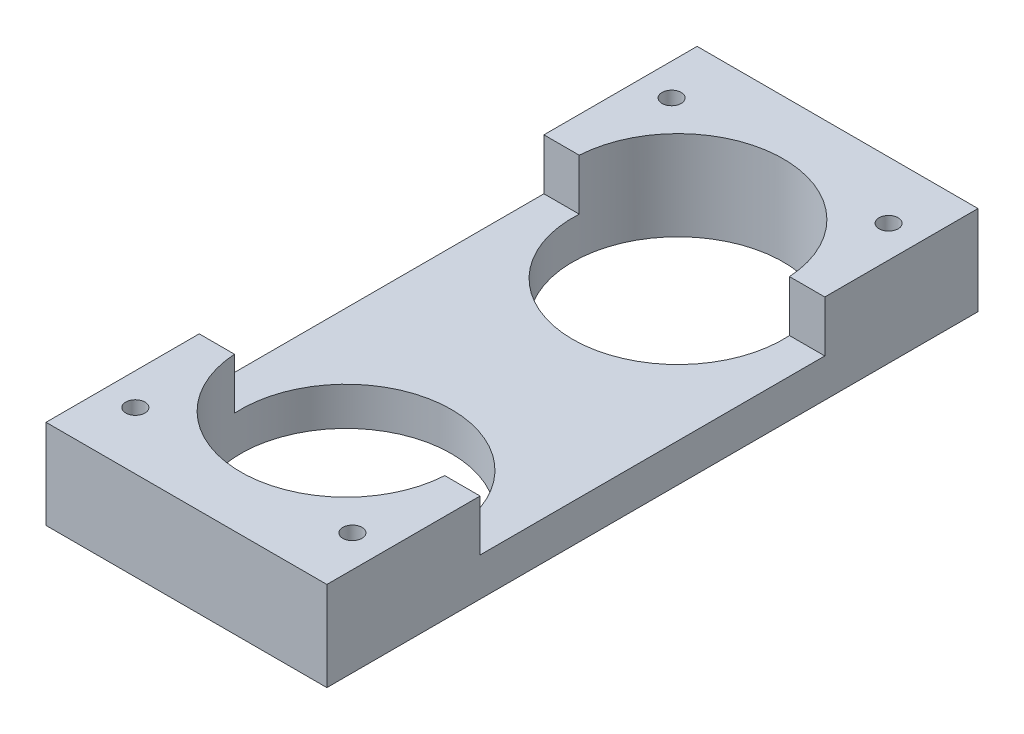
SolidWorks part; units mm, degrees
ref_plane "前视基准面" through (0, 0, 0) normal (0, 0, 1) x (1, 0, 0)
ref_plane "上视基准面" through (0, 0, 0) normal (0, 1, 0) x (1, 0, 0)
ref_plane "右视基准面" through (0, 0, 0) normal (1, 0, 0) x (0, 0, -1)
sketch "草图1" plane through (0, 0, 0) normal (0, 1, 0) x (1, 0, 0)
  line L1 (11, 25.5) -> (-11, 25.5)
  line L2 (11, 25.5) -> (11, -25.5)
  line L3 (11, -25.5) -> (-11, -25.5)
  line L4 (-11, 25.5) -> (-11, -25.5)
  line L5 (11, 25.5) -> (-11, -25.5) construction
  line L6 (11, -25.5) -> (-11, 25.5) construction
  point P0 (0, 0)
  dimension "D1" = 22
  dimension "D2" = 51
extrude "底座" add sketch "草图1" along normal blind 3
sketch "草图2" plane through (0, 3, 0) normal (0, 1, 0) x (1, 0, 0)
  line L0 (-11, 25.5) -> (-11, -25.5) construction
  line L1 (11, 13.5) -> (-11, 13.5)
  line L2 (11, 13.5) -> (11, -13.5)
  line L3 (11, -13.5) -> (-11, -13.5)
  line L4 (-11, 13.5) -> (-11, -13.5)
  line L5 (11, 13.5) -> (-11, -13.5) construction
  line L6 (11, -13.5) -> (-11, 13.5) construction
  point P0 (0, 0)
  line M2 (-11, 25.5) -> (-11, -25.5)
  line M3 (-11, -25.5) -> (11, -25.5)
  line M4 (11, -25.5) -> (11, 25.5)
  line M5 (11, 25.5) -> (-11, 25.5)
  dimension "D1" = 27
extrude "高台" add sketch "草图2" along normal blind 4 contours L3 M4 M2 M3 | L1 M4 M5 M2
sketch "草图3" plane through (0, 0, 0) normal (0, -1, 0) x (1, 0, 0)
  line L0 (11, 0) -> (-11, 0)
  line L1 (-11, -25.5) -> (-11, 25.5) construction
  circle A0 centre (0, 13) radius 8.25
  circle A1 centre (0, -13) radius 8.25
  point P8 (0, 0)
  dimension "D1" = 16.5
  dimension "D2" = 13
extrude "穿孔" cut sketch "草图3" against normal through all contours A0 | A1
sketch "草图4" plane through (0, 7, 0) normal (0, 1, 0) x (1, 0, 0)
  line L0 (11, 0) -> (-11, 0)
  line L1 (-11, 13.5) -> (-11, -13.5) construction
  line L2 (0, 25.5) -> (0, -25.5)
  line L3 (-11, -25.5) -> (11, -25.5) construction
  circle A0 centre (-8.5, -21) radius 0.75
  circle A1 centre (8.5, -21) radius 0.75
  circle A2 centre (8.5, 21) radius 0.75
  circle A3 centre (-8.5, 21) radius 0.75
  point P8 (0, 0)
  point P14 (0, 0)
  dimension "D1" = 1.5
  dimension "D2" = 8.5
  dimension "D3" = 21
extrude "螺丝口" cut sketch "草图4" against normal through all contours A0 | A1 | A3 | A2
